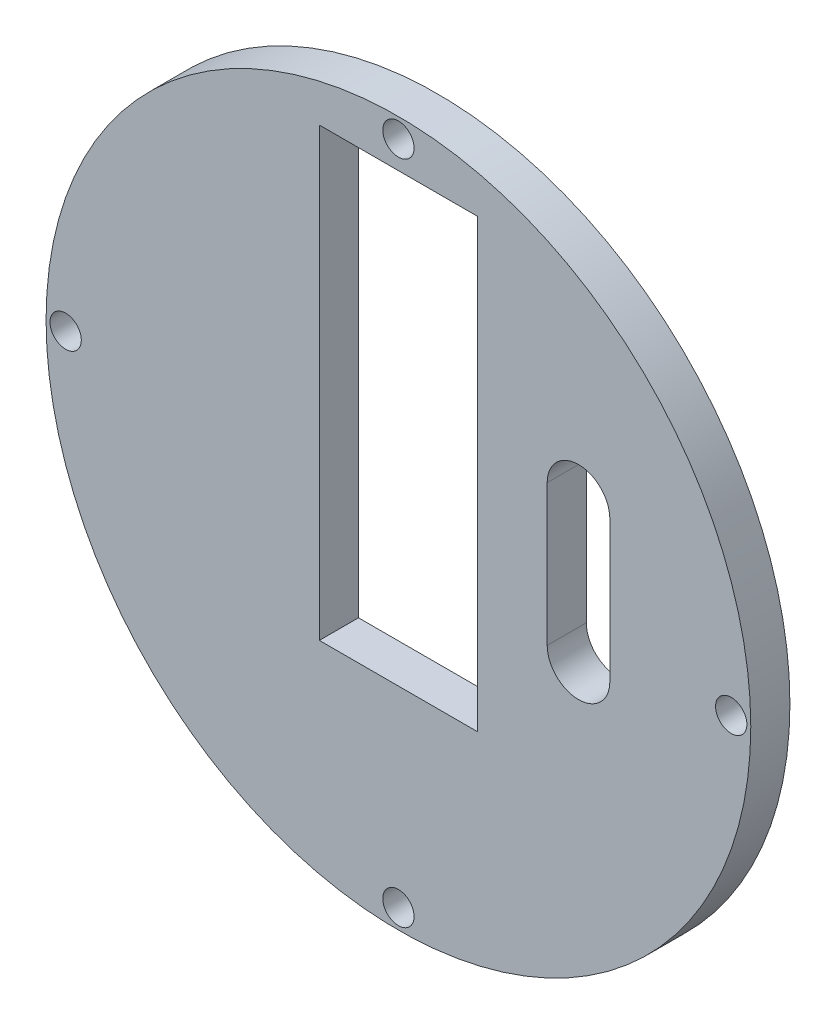
SolidWorks part; units mm, degrees
ref_plane "Front Plane" through (0, 0, 0) normal (0, 0, 1) x (1, 0, 0)
ref_plane "Top Plane" through (0, 0, 0) normal (0, 1, 0) x (1, 0, 0)
ref_plane "Right Plane" through (0, 0, 0) normal (1, 0, 0) x (0, 0, -1)
sketch "Sketch1" plane through (0, 0, 0) normal (0, 0, 1) x (1, 0, 0)
  line L0 (0, 61.1562) -> (0, -62.0155) construction
  line L1 (-10.1, 39) -> (10.1, 39)
  line L2 (-10.1, 39) -> (-10.1, -18)
  line L3 (-10.1, -18) -> (10.1, -18)
  line L4 (10.1, 39) -> (10.1, -18)
  line L5 (-10.1, 39) -> (10.1, -18) construction
  line L6 (-10.1, -18) -> (10.1, 39) construction
  line L7 (-62.9195, 0) -> (73.7046, 0) construction
  circle A0 centre (0, 0) radius 45
  circle A1 centre (0, 0) radius 1.25 construction
  circle A6 centre (42.5, 0) radius 2
  circle A7 centre (0, -42.5) radius 2
  circle A8 centre (-42.5, 0) radius 2
  circle A9 centre (0, 42.5) radius 2
  circle A10 centre (0, 0) radius 42.5 construction
  point P2 (0, 10.5)
  point P11 (5, -92.894)
  point P12 (5, 90.4881)
  point P13 (-96.2355, -5)
  point P14 (94.097, -5)
  point P15 (-5, -92.894)
  point P16 (-5, 90.4881)
  point P17 (-96.2355, 5)
  point P18 (94.097, 5)
  point P35 (0, 0)
  dimension "D1" = 90
  dimension "D5" = 2.5
  dimension "D14" = 4
  dimension "D13" = 85
  dimension "D2" = 20.2
  dimension "D3" = 57
  dimension "D15" = 4
  dimension "D4" = 18
extrude "Boss-Extrude1" add sketch "Sketch1" along normal blind 5
sketch "Sketch2" plane through (0, 0, 0) normal (0, 0, -1) x (-1, 0, 0)
  line L0 (-23, 14) -> (-23, -4) construction
  line L1 (-19, 14) -> (-19, -4)
  line L2 (-27, 14) -> (-27, -4)
  line L3 (10.1, 39) -> (-10.1, 39) construction
  arc A0 (-19, 14) -> (-27, 14) centre (-23, 14) ccw
  arc A1 (-27, -4) -> (-19, -4) centre (-23, -4) ccw
  point P2 (-23, 5)
  point P12 (-23, 18)
  dimension "D1" = 4
  dimension "D2" = 20.2
  dimension "D3" = 23
  dimension "D4" = 5
  dimension "D5" = 18
extrude "Cut-Extrude1" cut sketch "Sketch2" against normal blind 10
